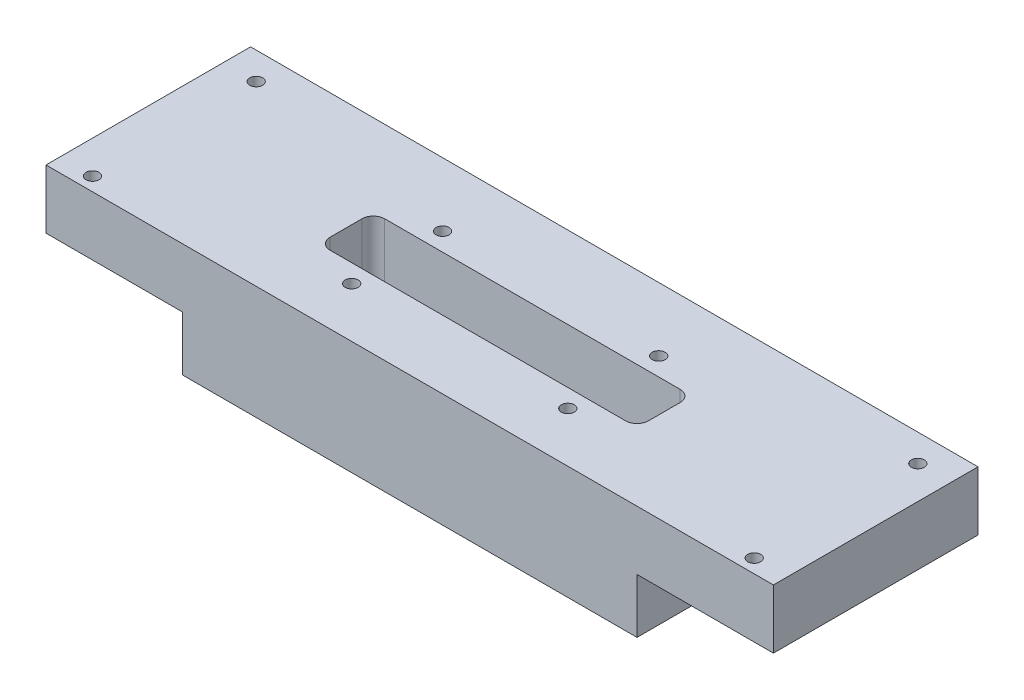
SolidWorks part; units mm, degrees
material "6061-T6 Al"
ref_plane "Front" through (0, 0, 0) normal (0, 0, 1) x (1, 0, 0)
ref_plane "Top" through (0, 0, 0) normal (0, 1, 0) x (1, 0, 0)
ref_plane "Right" through (0, 0, 0) normal (1, 0, 0) x (0, 0, -1)
sketch "Sketch1" plane through (0, 0, 0) normal (0, 1, 0) x (1, 0, 0)
  line L1 (-80, 22.5) -> (80, 22.5)
  line L2 (-80, 22.5) -> (-80, -22.5)
  line L3 (-80, -22.5) -> (80, -22.5)
  line L4 (80, 22.5) -> (80, -22.5)
  dimension "D1" = 80
  dimension "D2" = 80
  dimension "D3" = 22.5
  dimension "D4" = 22.5
extrude "Extrude1" add sketch "Sketch1" along normal blind 13
sketch "Sketch2" plane through (0, 0, 0) normal (0, -1, 0) x (1, 0, 0)
  line L0 (-80, 22.5) -> (80, 22.5) construction
  line L1 (-50, 22.5) -> (50, 22.5)
  line L2 (-50, 22.5) -> (-50, -22.5)
  line L3 (-50, -22.5) -> (50, -22.5)
  line L4 (50, 22.5) -> (50, -22.5)
  line L5 (80, -22.5) -> (-80, -22.5) construction
  line L6 (-80, -22.5) -> (-80, 22.5) construction
  line L7 (80, 22.5) -> (80, -22.5) construction
  dimension "D1" = 30
  dimension "D2" = 30
extrude "Extrude2" add sketch "Sketch2" along normal blind 12
ref_plane "Plane1" through (0, 0, 0) normal (1, 0, 0) x (0, 0, -1)
sketch "Sketch3" plane through (0, 13, 0) normal (0, 1, 0) x (1, 0, 0)
  line L0 (-80, -22.5) -> (80, -22.5) construction
  line L1 (-35, 4.5) -> (35, 4.5)
  line L2 (-35, 4.5) -> (-35, -7.5)
  line L3 (-35, -7.5) -> (35, -7.5)
  line L4 (35, 4.5) -> (35, -7.5)
  line L5 (80, 22.5) -> (-80, 22.5) construction
  line L6 (0, -13.145) -> (0, 13.145) construction
  dimension "D1" = 15
  dimension "D2" = 18
  dimension "D3" = 35
  dimension "D4" = 35
extrude "Extrude3" cut sketch "Sketch3" against normal through all
ref_plane "Plane2" through (0, 0, 1.5) normal (0, 0, -1) x (-1, 0, 0)
fillet "Fillet1" radius 2.5 4 edges at (35, 0.5, -4.5) (35, 0.5, 7.5) (-35, 0.5, 7.5) (-35, 0.5, -4.5)
hole_wizard "#4-40 Tapped Hole1" positions "3DSketch2" profile "Sketch5" tap size "#4-40" standard "Ansi Inch"
sketch3d "3DSketch2"
  point P0 (-72.77, 13, 19.5)
  point P2 (-23.77, 13, 11.5)
  point P4 (-23.77, 13, -8.5)
  point P6 (-72.77, 13, -16.5)
  dimension "D1" = 72.77
  dimension "D2" = 18
  dimension "D3" = 18
  dimension "D4" = 10
  dimension "D5" = 10
  dimension "D6" = 23.77
sketch "Sketch5" plane through (-72.77, 13, 19.5) normal (1, 0, 0) x (0, 0, 1)
  line L0 (0, 0) -> (0, 26.0538)
  line L1 (0, 26.0538) -> (1.1303, 25.3746)
  line L2 (1.1303, 25.3746) -> (1.1303, 5.6896)
  line L3 (1.1303, 5.6896) -> (1.4224, 5.6896)
  line L4 (1.4224, 5.6896) -> (1.4224, 0)
  line L5 (1.4224, 0) -> (0, 0)
  line L10 (0, 26.0538) -> (-1.1303, 25.3746) construction
  line L11 (0, -6.35) -> (0, 107.95) construction
  dimension "Tap Drill Dia." = 2.2606
  dimension "Tap Drill Depth" = 25.3746
  dimension "Thread Major Dia." = 2.8448
  dimension "Thread Depth" = 5.6896
  dimension "Drill Angle" = 118
mirror "Mirror1" about plane through (0, 0, 0) normal (1, 0, 0) of "#4-40 Tapped Hole1"
hole_wizard "1/4-20 Tapped Hole1" positions "3DSketch3" profile "Sketch6" tap size "1/4-20" standard "Ansi Inch"
sketch3d "3DSketch3"
  line L0 (50, -12, -22.5) -> (50, 0, -22.5) construction
  line L1 (50, 0, -22.5) -> (50, 0, 22.5) construction
  point P0 (50, -7, -14.5)
  point P2 (50, -7, 10.5)
  dimension "D1" = 8
  dimension "D2" = 33
  dimension "D3" = 7
sketch "Sketch6" plane through (50, -7, -14.5) normal (0, 1, 0) x (0, 0, -1)
  line L0 (0, 0) -> (0, 21.5338)
  line L1 (0, 21.5338) -> (2.5527, 20)
  line L2 (2.5527, 20) -> (2.5527, 12.7)
  line L3 (2.5527, 12.7) -> (3.175, 12.7)
  line L4 (3.175, 12.7) -> (3.175, 0)
  line L5 (3.175, 0) -> (0, 0)
  line L10 (0, 21.5338) -> (-2.5527, 20) construction
  line L11 (0, -6.35) -> (0, 107.95) construction
  dimension "Tap Drill Dia." = 5.1054
  dimension "Tap Drill Depth" = 20
  dimension "Thread Major Dia." = 6.35
  dimension "Thread Depth" = 12.7
  dimension "Drill Angle" = 118
sketch "Sketch7" plane through (0, -12, 0) normal (0, -1, 0) x (1, 0, 0)
  line L0 (50, -22.5) -> (50, 22.5) construction
  line L1 (-50, -22.5) -> (50, -22.5) construction
  circle A0 centre (31, -14.5) radius 0.75
  circle A1 centre (31, 10.5) radius 0.75
  dimension "D1" = 1.5
  dimension "D2" = 1.5
  dimension "D3" = 19
  dimension "D4" = 8
  dimension "D5" = 33
extrude "Extrude4" cut sketch "Sketch7" against normal blind 7
mirror "Mirror2" about plane through (0, 0, 0) normal (1, 0, 0) of "Extrude4", "1/4-20 Tapped Hole1"
hole_wizard "#4-40 Tapped Hole2" positions "Sketch9" profile "Sketch8" tap size "#4-40" standard "Ansi Inch"
sketch "Sketch9" plane through (0, 0, -22.5) normal (0, 0, -1) x (-1, 0, 0)
  line L0 (0, 13.75) -> (0, -13.75) construction
  line L1 (50, -12) -> (-50, -12) construction
  point P0 (-15, -9)
  dimension "D1" = 15
  dimension "D2" = 3
sketch "Sketch8" plane through (15, -9, -22.5) normal (1, 0, 0) x (0, 1, 0)
  line L0 (0, 0) -> (0, 20.9738)
  line L1 (0, 20.9738) -> (1.1303, 20.2946)
  line L2 (1.1303, 20.2946) -> (1.1303, 8.2296)
  line L3 (1.1303, 8.2296) -> (1.4224, 8.2296)
  line L4 (1.4224, 8.2296) -> (1.4224, 0)
  line L5 (1.4224, 0) -> (0, 0)
  line L10 (0, 20.9738) -> (-1.1303, 20.2946) construction
  line L11 (0, -6.35) -> (0, 107.95) construction
  dimension "Tap Drill Dia." = 2.2606
  dimension "Tap Drill Depth" = 20.2946
  dimension "Thread Major Dia." = 2.8448
  dimension "Thread Depth" = 8.2296
  dimension "Drill Angle" = 118
mirror "Mirror3" about plane through (0, 0, 0) normal (1, 0, 0) of "#4-40 Tapped Hole2"
equation "\"D6@3DSketch2\" = \"D1@3DSketch2\"-49/25.4"
equation "\"D2@Sketch7\" = \"D1@Sketch7\""
